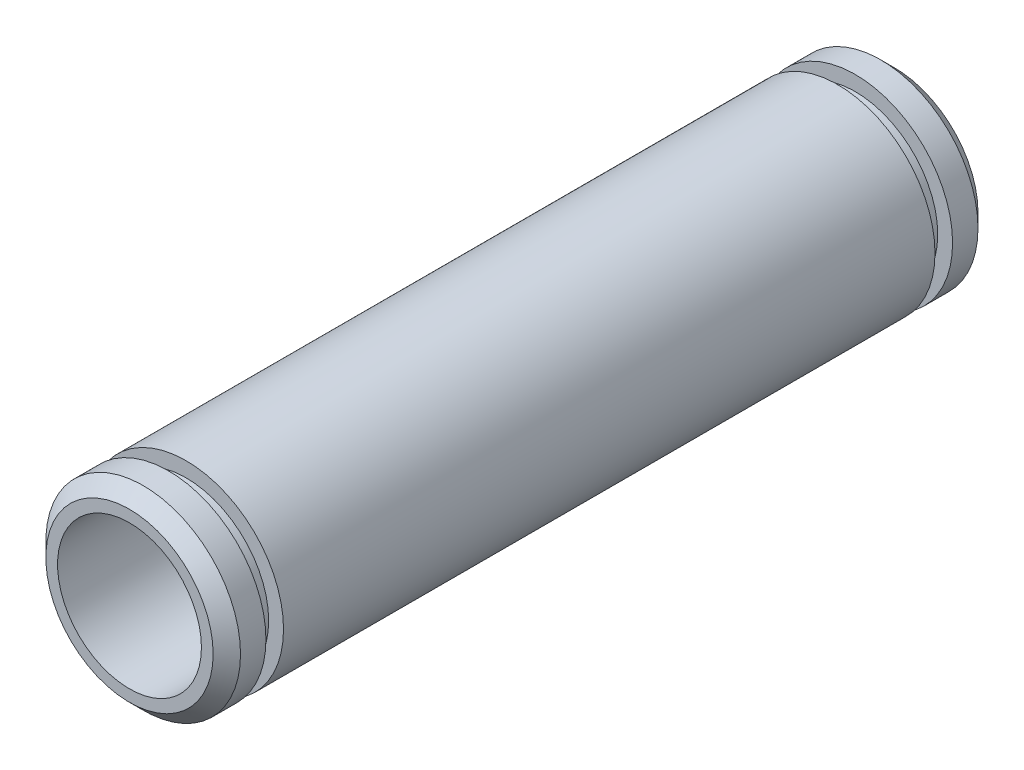
SolidWorks part; units mm, degrees
material "Commercial Bronze, UNS C22000 (90-10 Bronze)"
ref_plane "Front Plane" through (0, 0, 0) normal (0, 0, 1) x (1, 0, 0)
ref_plane "Top Plane" through (0, 0, 0) normal (0, 1, 0) x (1, 0, 0)
ref_plane "Right Plane" through (0, 0, 0) normal (1, 0, 0) x (0, 0, -1)
sketch "Sketch1" plane through (0, 0, 0) normal (0, 0, 1) x (1, 0, 0)
  circle A1 centre (0, 0) radius 6.3246
  circle A2 centre (0, 0) radius 4.6736
  dimension "D1" = 12.6492
  dimension "D2" = 1.651
extrude "Boss-Extrude1" add sketch "Sketch1" along normal mid plane 49.6951
sketch "Sketch2" plane through (0, 0, 0) normal (0, 1, 0) x (1, 0, 0)
  line L0 (6.3246, -24.8475) -> (6.3246, 24.8475) construction
  line L1 (6.3246, 22.3075) -> (5.3594, 22.3075)
  line L2 (6.3246, 22.3075) -> (6.3246, 21.1645)
  line L3 (6.3246, 21.1645) -> (5.3594, 21.1645)
  line L4 (5.3594, 22.3075) -> (5.3594, 21.1645)
  line L5 (6.3246, 24.8475) -> (-6.3246, 24.8475) construction
  line L6 (0, -1000) -> (0, 49000) construction
  dimension "D1" = 1.143
  dimension "D2" = 2.54
  dimension "D3" = 0.9652
revolve "Cut-Revolve1" cut sketch "Sketch2" angle 360 about L6
mirror "Mirror1" about plane through (0, 0, 0) normal (0, 0, 1) of "Cut-Revolve1"
chamfer "Chamfer1" distance 0.889 angle 45 2 edges at (6.3246, 0, 24.8475) (6.3246, 0, -24.8475)
